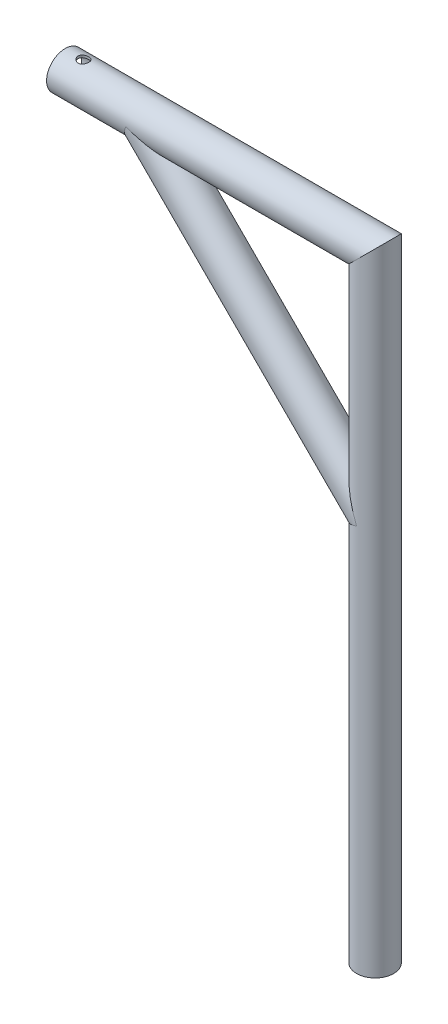
SolidWorks part; units mm, degrees
ref_plane "Front Plane" through (0, 0, 0) normal (0, 0, 1) x (1, 0, 0)
ref_plane "Top Plane" through (0, 0, 0) normal (0, 1, 0) x (1, 0, 0)
ref_plane "Right Plane" through (0, 0, 0) normal (1, 0, 0) x (0, 0, -1)
sketch "Sketch1" plane through (0, 0, 0) normal (0, 0, 1) x (1, 0, 0)
  line L0 (0, 0) -> (0, 798)
  line L1 (0, 798) -> (-400, 798)
  dimension "D1" = 798
  dimension "D2" = 400
sketch "Sketch2" plane through (0, 0, 0) normal (0, 1, 0) x (1, 0, 0)
  circle A0 centre (0, 0) radius 24
sweep "Sweep-Thin1" add profiles "Sketch2" path "Sketch1" parameters "D1"=3
ref_plane "Plane1" through (-399, 399, 0) normal (0.7071, -0.7071, 0) x (0, 0, -1)
sketch "Sketch3" plane through (-399, 399, 0) normal (0.7071, -0.7071, 0) x (0, 0, -1)
  circle A0 centre (0, 353.7819) radius 24
  point P2 (0, 377.9902)
  point P3 (0, 353.7819)
  dimension "D1" = 48
extrude "Extrude-Thin4" add sketch "Sketch3" along normal up to next and the other way up to next thin thin type one direction reverse wall 2
sketch "Sketch4" plane through (0, 0, 0) normal (0, 1, 0) x (1, 0, 0)
  line L0 (-400, 0) -> (-267.9397, 0) construction
  line L1 (-400, 24) -> (-400, -24) construction
  circle A0 centre (-376.34, 0) radius 7
  dimension "D1" = 23.66
extrude "Cut-Extrude1" cut sketch "Sketch4" along normal through all
